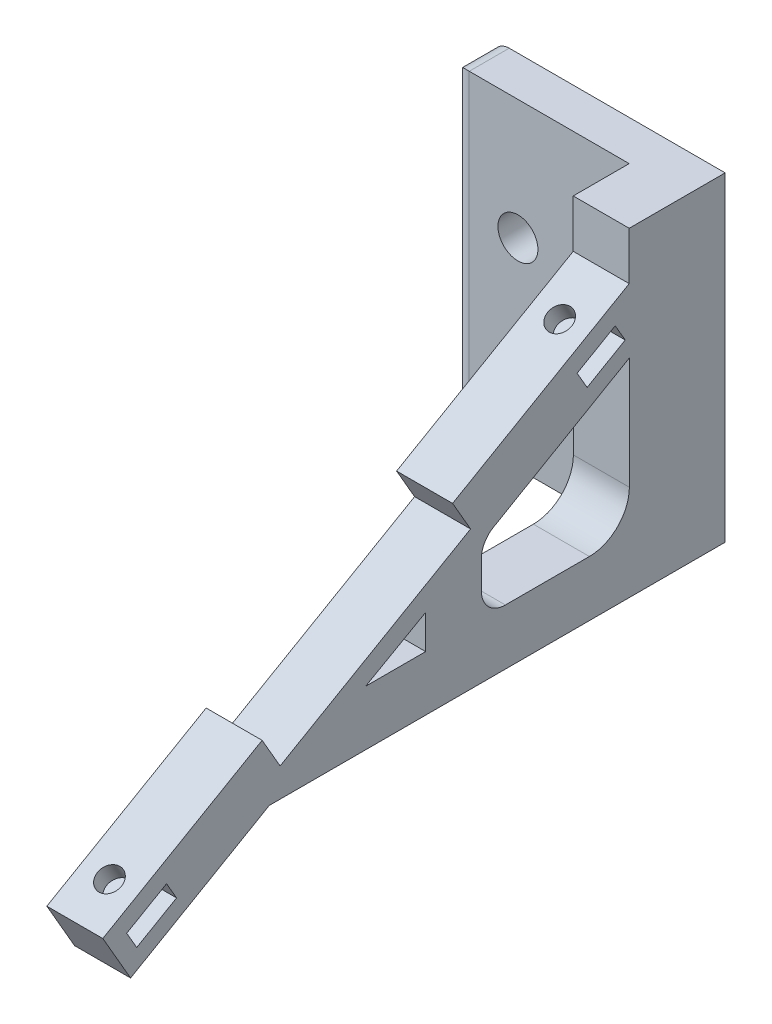
SolidWorks part; units mm, degrees
ref_plane "Front Plane" through (0, 0, 0) normal (0, 0, 1) x (1, 0, 0)
ref_plane "Top Plane" through (0, 0, 0) normal (0, 1, 0) x (1, 0, 0)
ref_plane "Right Plane" through (0, 0, 0) normal (1, 0, 0) x (0, 0, -1)
sketch "Sketch1" plane through (0, 0, 0) normal (1, 0, 0) x (0, 0, -1)
  line L0 (0, 0) -> (0, 40)
  line L1 (0, 40) -> (-7, 40)
  line L2 (-7, 40) -> (-7, 34)
  line L3 (-7, 34) -> (-29.0836, 21.25)
  line L4 (-29.0836, 21.25) -> (-26.8336, 17.3529)
  line L5 (-26.8336, 17.3529) -> (-50.6493, 3.6029)
  line L6 (-50.6493, 3.6029) -> (-52.8993, 7.5)
  line L7 (-52.8993, 7.5) -> (-72.8179, -4)
  line L8 (-72.8179, -4) -> (-69.3455, -10.0144)
  line L9 (-69.3455, -10.0144) -> (-52, 0)
  line L10 (-52, 0) -> (0, 0)
  line L11 (-69.8283, -4.9261) -> (-64.8487, -2.0511)
  line L12 (-64.8487, -2.0511) -> (-63.5987, -4.2162)
  line L13 (-63.5987, -4.2162) -> (-68.5783, -7.0912)
  line L14 (-68.5783, -7.0912) -> (-69.8283, -4.9261)
  line L15 (-39.9499, 6.884) -> (-32.4499, 11.134)
  line L16 (-32.4499, 11.134) -> (-32.4499, 6.884)
  line L17 (-32.4499, 6.884) -> (-39.9499, 6.884)
  line L18 (-6.98, 25.947) -> (-6.98, 11.947)
  line L19 (-11.98, 6.947) -> (-22.48, 6.947)
  line L20 (-25.48, 9.947) -> (-25.48, 13.5056)
  line L21 (-6.98, 25.947) -> (-23.98, 16.107)
  line L22 (-13.5125, 27.5567) -> (-8.7524, 30.3119)
  line L23 (-8.7524, 30.3119) -> (-7.5, 28.1483)
  line L24 (-7.5, 28.1483) -> (-12.2601, 25.393)
  line L25 (-12.2601, 25.393) -> (-13.5125, 27.5567)
  arc A0 (-6.98, 11.947) -> (-11.98, 6.947) centre (-11.98, 11.947) cw
  arc A1 (-22.48, 6.947) -> (-25.48, 9.947) centre (-22.48, 9.947) cw
  arc A2 (-25.48, 13.5056) -> (-23.98, 16.107) centre (-22.4743, 13.5056) cw
  dimension "D19" = 5
  dimension "D20" = 3
  dimension "D22" = 9.84
  dimension "D1" = 40
  dimension "D2" = 7
  dimension "D3" = 6
  dimension "D4" = 25.5
  dimension "D5" = 4.5
  dimension "D6" = 27.5
  dimension "D7" = 4.5
  dimension "D8" = 23
  dimension "D9" = 52
  dimension "D10" = 150
  dimension "D11" = 2.148
  dimension "D12" = 2.126
  dimension "D13" = 2.5
  dimension "D14" = 5.75
  dimension "D15" = 7.5
  dimension "D16" = 4.25
  dimension "D17" = 32.868
  dimension "D18" = 6.884
  dimension "D21" = 10.5
  dimension "D23" = 17
  dimension "D24" = 11.98
  dimension "D25" = 25.947
  dimension "D26" = 19
  dimension "D27" = 5.5
  dimension "D28" = 2.5
  dimension "D29" = 7.5
  dimension "D30" = 25.393
extrude "Boss-Extrude1" add sketch "Sketch1" against normal blind 7
sketch "Sketch2" plane through (0, 0, 0) normal (0, 0, -1) x (-1, 0, 0)
  line L0 (0, 40) -> (29, 40)
  line L1 (29, 40) -> (29, 0)
  line L2 (29, 0) -> (0, 0)
  line L3 (0, 0) -> (0, 40)
  line L4 (20.9125, 5) -> (20.9125, 25) construction
  circle A0 centre (20.9125, 25) radius 2.5
  circle A1 centre (20.9125, 5) radius 2.5
  dimension "D2" = 5
  dimension "D3" = 5
  dimension "D1" = 29
  dimension "D4" = 35
  dimension "D5" = 20
  dimension "D6" = 8.0875
extrude "Boss-Extrude2" add sketch "Sketch2" along normal blind 5
fillet "Fillet1" radius 2 3 edges at (-29, 0, -2.5) (-29, 20, 0) (-29, 40, -2.5)
sketch "Sketch3" plane through (0, 28.5311, 16.4724) normal (0, 0.866, 0.5) x (1, 0, 0)
  line L0 (-3.5, 4.9378) -> (-3.5, -60.0622) construction
  line L1 (-7, 10.9378) -> (0, 10.9378) construction
  line L2 (0, 10.9378) -> (0, -14.5622) construction
  circle A0 centre (-3.5, 4.9378) radius 1.5
  circle A1 centre (-3.5, -60.0622) radius 1.5
  dimension "D1" = 3
  dimension "D2" = 3
  dimension "D3" = 65
  dimension "D4" = 6
  dimension "D5" = 3.5
extrude "Cut-Extrude1" cut sketch "Sketch3" against normal blind 7.5
